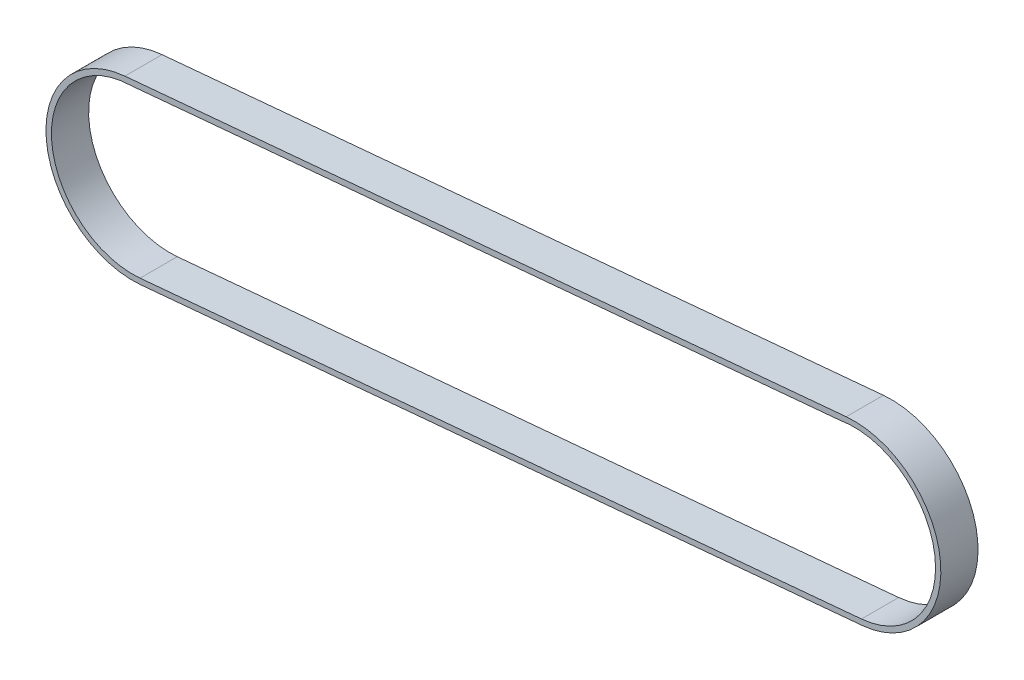
SolidWorks part; units mm, degrees
ref_plane "Ön Düzlem" through (0, 0, 0) normal (0, 0, 1) x (1, 0, 0)
ref_plane "Üst Düzlem" through (0, 0, 0) normal (0, 1, 0) x (1, 0, 0)
ref_plane "Sağ Düzlem" through (0, 0, 0) normal (1, 0, 0) x (0, 0, -1)
sketch "Çizim1" plane through (0, 0, 0) normal (0, 0, 1) x (-1, 0, 0)
  line L1 (-215.4971, -78) -> (75.5029, -51.5) construction
  line L2 (-218.6712, -43.1442) -> (72.3288, -16.6442)
  line L3 (-212.3229, -112.8558) -> (78.6771, -86.3558)
  line L4 (-218.4703, -45.2753) -> (72.5353, -18.8362)
  line L5 (-210.6832, -110.4431) -> (76.1681, -84.2916)
  arc A0 (-218.6712, -43.1442) -> (-212.3229, -112.8558) centre (-215.4971, -78) ccw
  arc A1 (78.6771, -86.3558) -> (72.3288, -16.6442) centre (75.5029, -51.5) ccw
  arc A2 (-218.4703, -45.2753) -> (-209.8089, -110.3634) centre (-215.4971, -78) ccw
  arc A3 (76.1681, -84.2916) -> (72.5353, -18.8362) centre (75.5029, -51.5) ccw
extrude "Yükseklik-Ekstrüzyon1" add sketch "Çizim1" along normal mid plane 15 contours L3 A1 L2 A0 A3 L5 A2 L4
